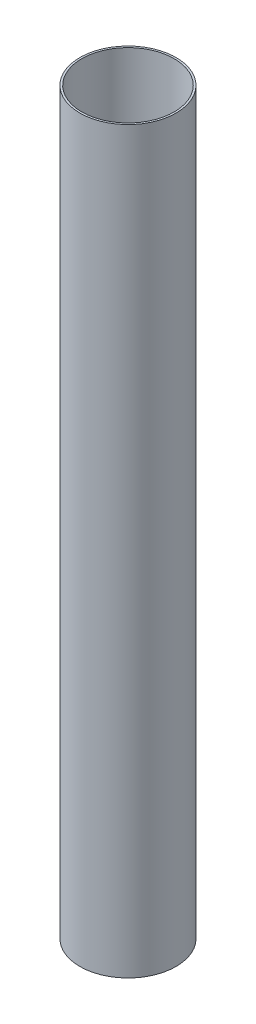
SolidWorks part; units mm, degrees
material "S-Glass Fiber"
ref_plane "Front Plane" through (0, 0, 0) normal (0, 0, 1) x (1, 0, 0)
ref_plane "Top Plane" through (0, 0, 0) normal (0, 1, 0) x (1, 0, 0)
ref_plane "Right Plane" through (0, 0, 0) normal (1, 0, 0) x (0, 0, -1)
other "Center of Mass"
sketch "Sketch2" plane through (0, 0, 0) normal (0, 1, 0) x (1, 0, 0)
  circle A0 centre (0, 0) radius 79.375
  circle A1 centre (0, 0) radius 76.2
  dimension "D1" = 152.4
  dimension "D2" = 158.75
extrude "Boss-Extrude1" add sketch "Sketch2" along normal blind 1219.2
